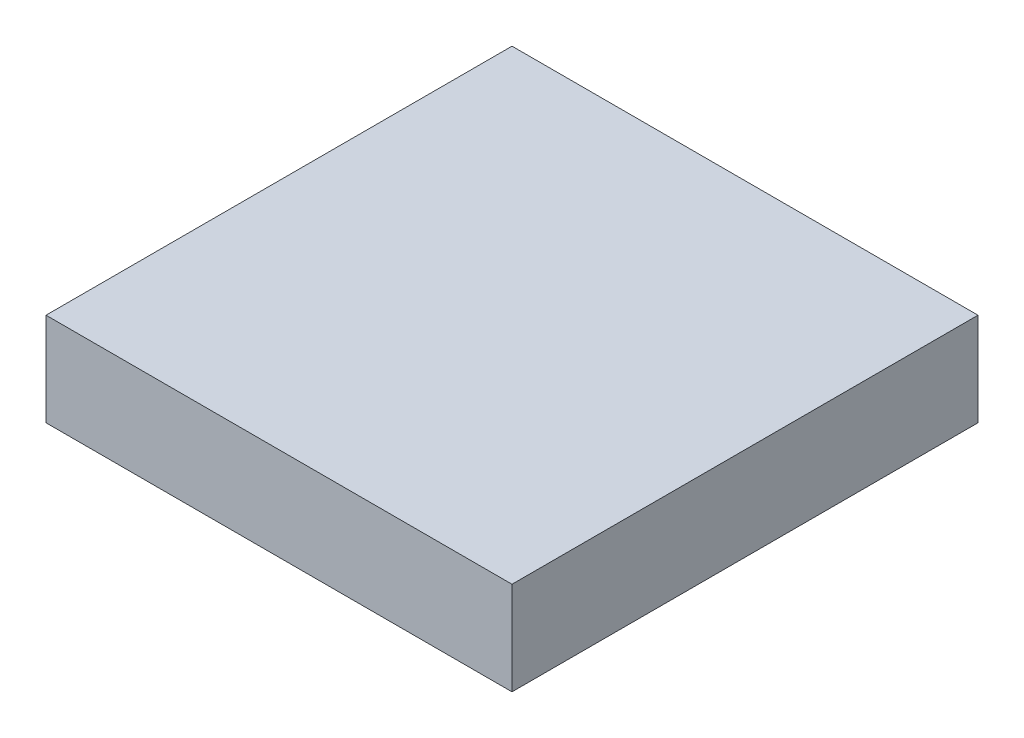
SolidWorks part; units mm, degrees
ref_plane "Front Plane" through (0, 0, 0) normal (0, 0, 1) x (1, 0, 0)
ref_plane "Top Plane" through (0, 0, 0) normal (0, 1, 0) x (1, 0, 0)
ref_plane "Right Plane" through (0, 0, 0) normal (1, 0, 0) x (0, 0, -1)
sketch "Sketch1" plane through (0, 0, 0) normal (0, 1, 0) x (1, 0, 0)
  line L1 (-7.5, -7.5) -> (7.5, -7.5)
  line L2 (-7.5, -7.5) -> (-7.5, 7.5)
  line L3 (-7.5, 7.5) -> (7.5, 7.5)
  line L4 (7.5, -7.5) -> (7.5, 7.5)
  line L5 (-7.5, -7.5) -> (7.5, 7.5) construction
  line L6 (-7.5, 7.5) -> (7.5, -7.5) construction
  point P0 (0, 0)
  dimension "D1" = 15
  dimension "D2" = 15
extrude "Boss-Extrude1" add sketch "Sketch1" along normal blind 3
sketch "Sketch2" plane through (0, 0, 0) normal (0, -1, 0) x (1, 0, 0)
  circle A0 centre (0, 0) radius 2.5
  circle A1 centre (0, 0) radius 6
  dimension "D1" = 5
  dimension "D2" = 12
extrude "Cut-Extrude1" cut sketch "Sketch2" against normal blind 2
sketch "Sketch3" plane through (0, 0, 0) normal (0, -1, 0) x (1, 0, 0)
  line L0 (7.5, 7.5) -> (7.5, -7.5) construction
  line L1 (7.5, -7.5) -> (-7.5, -7.5) construction
  line L2 (-7.5, -7.5) -> (-7.5, 7.5) construction
  line L3 (-7.5, 7.5) -> (7.5, 7.5) construction
  circle A0 centre (-5.5, 5.5) radius 1.25
  circle A1 centre (5.5, 5.5) radius 1.25
  circle A2 centre (5.5, -5.5) radius 1.25
  circle A3 centre (-5.5, -5.5) radius 1.25
  dimension "D1" = 2.5
  dimension "D2" = 2.5
  dimension "D3" = 2.5
  dimension "D4" = 2.5
  dimension "D5" = 2
  dimension "D6" = 2
  dimension "D7" = 2
  dimension "D8" = 2
  dimension "D9" = 2
  dimension "D10" = 2
  dimension "D11" = 2
  dimension "D12" = 2
extrude "Cut-Extrude2" cut sketch "Sketch3" against normal blind 2
